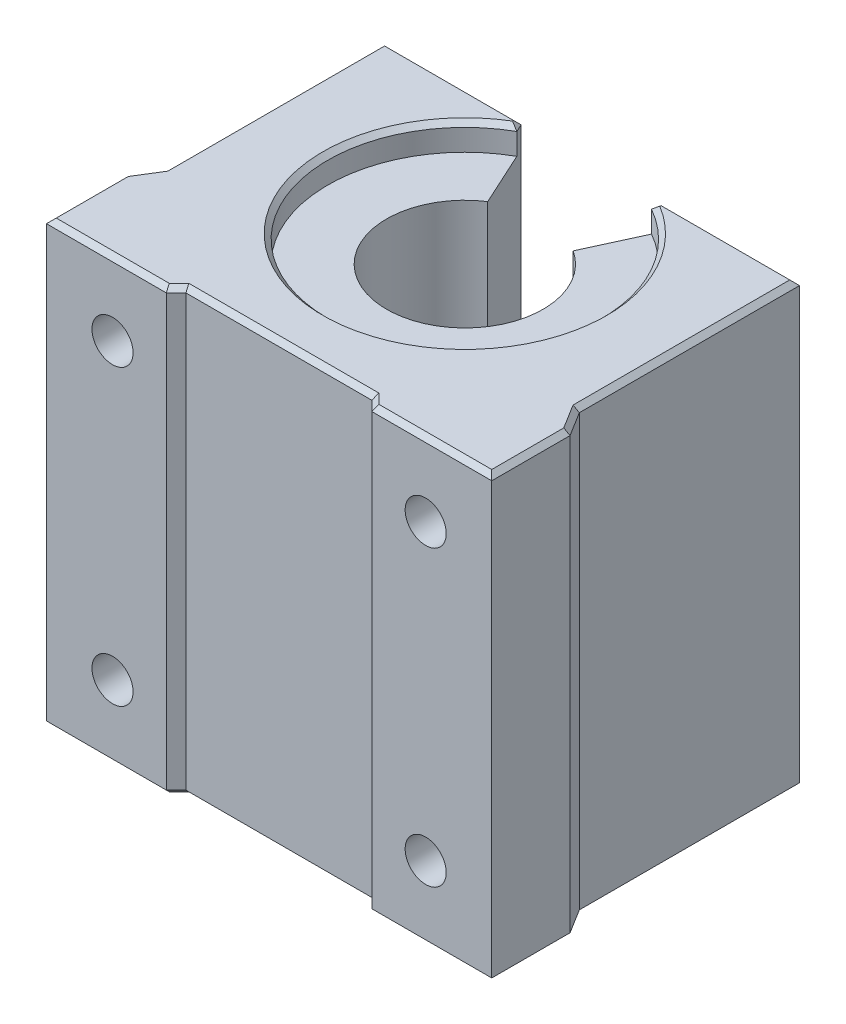
SolidWorks part; units mm, degrees
ref_plane "Front Plane" through (0, 0, 0) normal (0, 0, 1) x (1, 0, 0)
ref_plane "Top Plane" through (0, 0, 0) normal (0, 1, 0) x (1, 0, 0)
ref_plane "Right Plane" through (0, 0, 0) normal (1, 0, 0) x (0, 0, -1)
ref_plane "Plane1" through (0, 0, -13.05) normal (0, 0, -1) x (-1, 0, 0)
sketch "Sketch1" plane through (0, 0, -13.05) normal (0, 0, -1) x (-1, 0, 0)
  line L0 (22.75, 22.5) -> (-22.75, 22.5)
  line L1 (-22.75, 22.5) -> (-22.75, -22.5)
  line L2 (-22.75, -22.5) -> (22.75, -22.5)
  line L3 (22.75, -22.5) -> (22.75, 22.5)
  line L4 (-22.75, 22.5) -> (22.75, -22.5) construction
  dimension "D1" = 45.5
  dimension "D2" = 45
extrude "Boss-Extrude1" add sketch "Sketch1" against normal blind 33
sketch "Sketch2" plane through (0, 22.5, 0) normal (0, 1, 0) x (-1, 0, 0)
  line L0 (-21.2, -13.05) -> (-21.2, 9.45)
  line L1 (-21.2, 9.45) -> (-22.75, 11.95)
  line L2 (-22.75, 11.95) -> (-22.75, -13.05)
  line L3 (-22.75, -13.05) -> (-21.2, -13.05)
  line L4 (22.75, 19.95) -> (-22.75, 19.95) construction
  dimension "D1" = 21.2
  dimension "D2" = 8
  dimension "D3" = 10.5
extrude "Cut-Extrude1" cut sketch "Sketch2" against normal through all
mirror "Mirror1" about plane through (0, 0, 0) normal (1, 0, 0) of "Cut-Extrude1"
sketch "Sketch3" plane through (0, 22.5, 0) normal (0, 1, 0) x (-1, 0, 0)
  line L0 (-10.5, 19.95) -> (-9.5, 18.95)
  line L1 (-9.5, 18.95) -> (9.5, 18.95)
  line L2 (9.5, 18.95) -> (10.5, 19.95)
  line L3 (10.5, 19.95) -> (-10.5, 19.95)
  point P4 (0, 18.95)
  point P6 (0, 0)
  point P8 (-8.35, 18.85)
  point P9 (0, 0)
  dimension "D1" = 21
  dimension "D2" = 19
  dimension "D3" = 1
extrude "Cut-Extrude2" cut sketch "Sketch3" against normal through all
sketch "Sketch5" plane through (0, 22.5, 0) normal (0, 1, 0) x (-1, 0, 0)
  line L0 (-7.25, -13.05) -> (7.25, -13.05)
  line L1 (7.25, -13.05) -> (0, 2.7682)
  line L2 (0, 2.7682) -> (-7.25, -13.05)
  line L3 (21.2, -13.05) -> (-21.2, -13.05) construction
  point P3 (0, -13.05)
  point P5 (0, 0)
  point P6 (7.25, -13.05)
  point P9 (7.25, -13.05)
  point P10 (0, 2.7682)
  dimension "D1" = 14.5
  dimension "D2" = 15.8182
extrude "Cut-Extrude4" cut sketch "Sketch5" against normal through all
ref_plane "Plane2" through (0, 0, -0.05) normal (0, 0, 1) x (1, 0, 0)
sketch "Sketch6" plane through (0, 0, -0.05) normal (0, 0, 1) x (1, 0, 0)
  line L0 (14, 22.5) -> (0, 22.5)
  line L1 (0, 22.5) -> (0, -22.5)
  line L2 (0, -22.5) -> (14, -22.5)
  line L3 (14, -22.5) -> (14, -19.8)
  line L4 (14, -19.8) -> (8, -19.8)
  line L5 (8, -19.8) -> (8, 19.8)
  line L6 (8, 19.8) -> (14, 19.8)
  line L7 (14, 19.8) -> (14, 22.5)
  line L8 (0, 22.5) -> (0, -22.5) construction
  point P8 (0, 0)
  point P10 (0, 0)
  point P11 (0, 0)
  point P13 (0, 0)
  dimension "D1" = 14
  dimension "D2" = 8
  dimension "D3" = 2.7
revolve "Cut-Revolve1" cut sketch "Sketch6" angle 360 about L8
hole_wizard "M5x0.8 Tapped Hole1" positions "Sketch8" profile "Sketch7" tap size "M5x0.8" standard "ANSI Metric"
sketch "Sketch8" plane through (0, 0, 19.95) normal (0, 0, 1) x (1, 0, 0)
  line L0 (16, 15) -> (-16, -15) construction
  line L2 (22.75, 22.5) -> (22.75, -22.5) construction
  line L3 (22.75, 22.5) -> (22.75, -22.5) construction
  point P0 (-16, -15)
  point P1 (16, 15)
  point P2 (16, -15)
  point P3 (-16, 15)
  point P12 (0, 0)
  point P18 (22.75, 0)
  dimension "D1" = 32
  dimension "D2" = 30
sketch "Sketch7" plane through (-16, -15, 19.95) normal (1, 0, 0) x (0, -1, 0)
  line L0 (0, 0) -> (0, 16.8618)
  line L1 (0, 16.8618) -> (2.1, 15.6)
  line L2 (2.1, 15.6) -> (2.1, 0)
  line L5 (2.1, 0) -> (0, 0)
  line L10 (0, 16.8618) -> (-2.1, 15.6) construction
  line L11 (0, -6.35) -> (0, 107.95) construction
  dimension "Tap Drill Dia." = 4.2
  dimension "Tap Drill Depth" = 15.6
  dimension "Drill Angle" = 118
chamfer "Chamfer1" distance 0.5 angle 45 32 edges at (-7.065, -22.5, -12.6464) (-14.225, -22.5, -13.05) (-21.2, -22.5, -1.8) (-21.975, -22.5, 10.7) (-22.75, -22.5, 15.95) (-16.625, -22.5, 19.95) (-10, -22.5, 19.45) (0, -22.5, 18.95) (10, -22.5, 19.45) (16.625, -22.5, 19.95) (22.75, -22.5, 15.95) (21.975, -22.5, 10.7) (21.2, -22.5, -1.8) (14.225, -22.5, -13.05) (7.065, -22.5, -12.6464) (0, -22.5, 13.95) (7.065, 22.5, -12.6464) (14.225, 22.5, -13.05) (21.2, 22.5, -1.8) (21.975, 22.5, 10.7) (22.75, 22.5, 15.95) (16.625, 22.5, 19.95) (10, 22.5, 19.45) (0, 22.5, 18.95) (-10, 22.5, 19.45) (-16.625, 22.5, 19.95) (-22.75, 22.5, 15.95) (-21.975, 22.5, 10.7) (-21.2, 22.5, -1.8) (-14.225, 22.5, -13.05) (-7.065, 22.5, -12.6464) (0, 22.5, 13.95)
